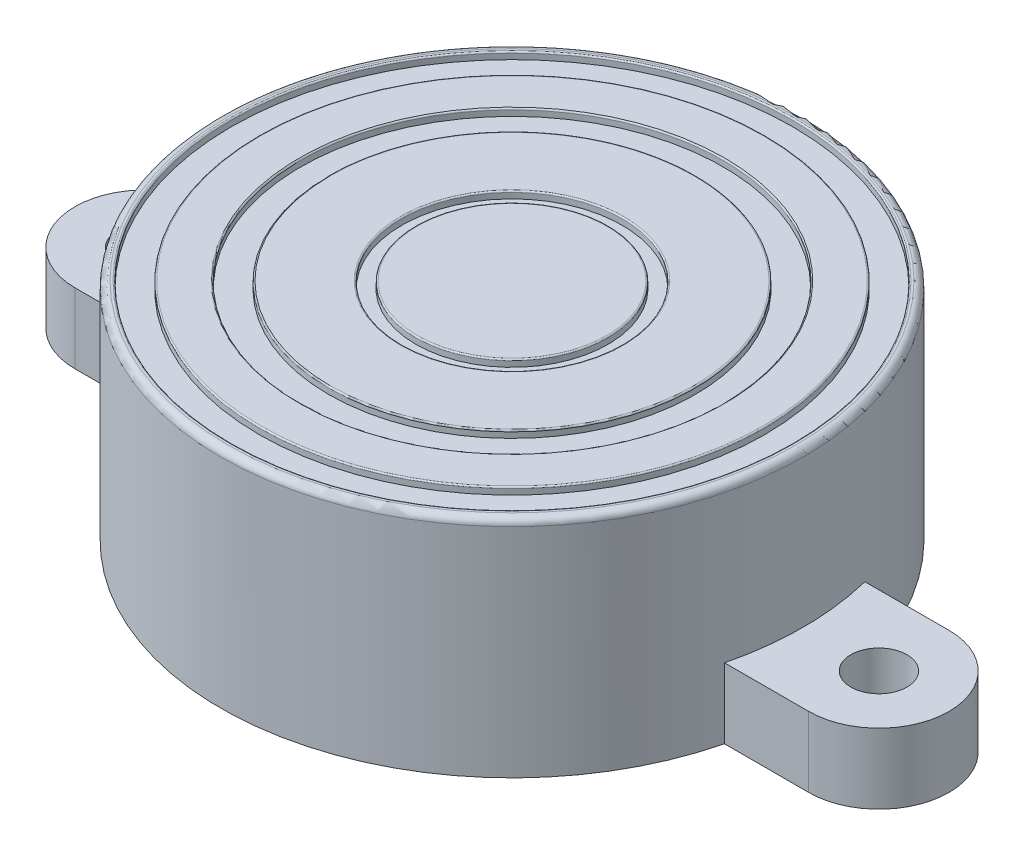
SolidWorks part; units mm, degrees
ref_plane "Front Plane" through (0, 0, 0) normal (0, 0, 1) x (1, 0, 0)
ref_plane "Top Plane" through (0, 0, 0) normal (0, 1, 0) x (1, 0, 0)
ref_plane "Right Plane" through (0, 0, 0) normal (1, 0, 0) x (0, 0, -1)
sketch "Sketch1" plane through (0, 0, 0) normal (0, 1, 0) x (1, 0, 0)
  circle A0 centre (0, 0) radius 20.75
  dimension "D1" = 41.5
extrude "Boss-Extrude1" add sketch "Sketch1" along normal blind 16
sketch "Sketch2" plane through (0, 16, 0) normal (0, 1, 0) x (1, 0, 0)
  circle A0 centre (0, 0) radius 6.85
  circle A1 centre (0, 0) radius 7.85
  circle A2 centre (0, 0) radius 13.05
  circle A3 centre (0, 0) radius 15.05
  circle A4 centre (0, 0) radius 18
  circle A5 centre (0, 0) radius 20
  dimension "D1" = 13.7
  dimension "D2" = 15.7
  dimension "D3" = 26.1
  dimension "D4" = 2
  dimension "D5" = 36
  dimension "D6" = 2
extrude "Cut-Extrude1" cut sketch "Sketch2" against normal blind 0.5 contours A1 A0 | A3 A2 | A5 A4
fillet "Fillet1" radius 0.1 6 edges at (0, 16, 20) (0, 16, 18) (0, 16, 15.05) (0, 16, 13.05) (0, 16, 6.85) (0, 16, 7.85)
fillet "Fillet2" radius 0.5 1 edges at (0, 16, 20.75)
sketch "Sketch3" plane through (0, 0, 0) normal (0, -1, 0) x (1, 0, 0)
  line L0 (0, -5) -> (0, 5) construction
  line L1 (20.1386, -5) -> (-20.1386, -5) construction
  line L2 (20.1386, 5) -> (-20.1386, 5) construction
  line L3 (-20.1386, -5) -> (-26.1386, -5)
  line L4 (-20.1386, 5) -> (-26.1386, 5)
  line L5 (20.1386, -5) -> (26.1386, -5)
  line L6 (20.1386, 5) -> (26.1386, 5)
  circle A2 centre (0, 0) radius 20.75 construction
  circle A3 centre (26.1386, 0) radius 5
  circle A4 centre (-26.1386, 0) radius 5
  point P4 (0, 0)
  point P11 (0, -5)
  point P14 (0, 5)
  circle M6 centre (0, 0) radius 20.75
  dimension "D3" = 10
  dimension "D1" = 10
  dimension "D2" = 6
extrude "Boss-Extrude2" add sketch "Sketch3" against normal blind 5 contours A4 L3 L4 M6 | A3 L6 L5 M6 | A4 | A3 A4
sketch "Sketch4" plane through (0, 5, 0) normal (0, 1, 0) x (1, 0, 0)
  line L0 (-20.1386, -5) -> (-26.1386, -5) construction
  circle A0 centre (26.1386, 0) radius 2
  circle A1 centre (-26.1386, 0) radius 2
  arc A2 (-26.1386, 5) -> (-26.1386, -5) centre (-26.1386, 0) ccw construction
  arc A4 (26.1386, -5) -> (26.1386, 5) centre (26.1386, 0) ccw construction
  point P7 (-31.1386, 0)
  point P14 (31.1386, 0)
  dimension "D5" = 4
  dimension "D1" = 5
  dimension "D2" = 5
  dimension "D3" = 5
  dimension "D4" = 5
extrude "Cut-Extrude2" cut sketch "Sketch4" against normal up to surface (5 mm away) up to face at (0, 0, 0)
